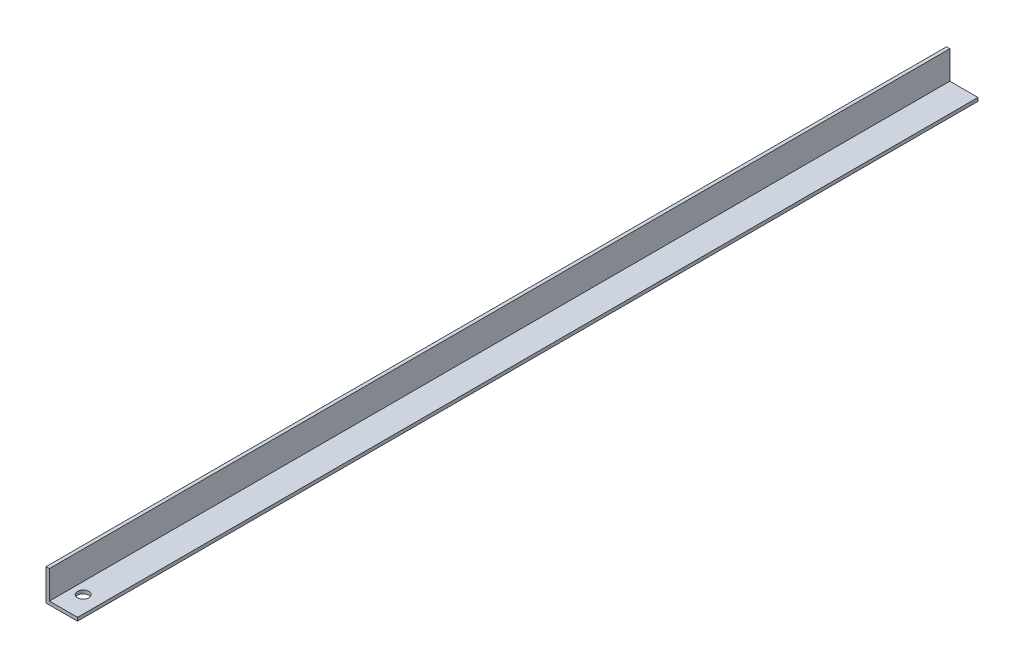
SolidWorks part; units mm, degrees
ref_plane "Спереди" through (0, 0, 0) normal (0, 0, 1) x (1, 0, 0)
ref_plane "Сверху" through (0, 0, 0) normal (0, 1, 0) x (1, 0, 0)
ref_plane "Справа" through (0, 0, 0) normal (1, 0, 0) x (0, 0, -1)
sketch "Эскиз1" plane through (0, 0, 0) normal (0, 0, 1) x (1, 0, 0)
  line L0 (0, 25) -> (0, 0)
  line L1 (0, 0) -> (25, 0)
extrude "Вытянуть-Тонкостенный1" add sketch "Эскиз1" along normal blind 800 thin
sketch "Эскиз2" plane through (0, -3, 0) normal (0, -1, 0) x (1, 0, 0)
  circle A0 centre (10, 780) radius 5
extrude "Вырез-Вытянуть1" cut sketch "Эскиз2" against normal blind 10
